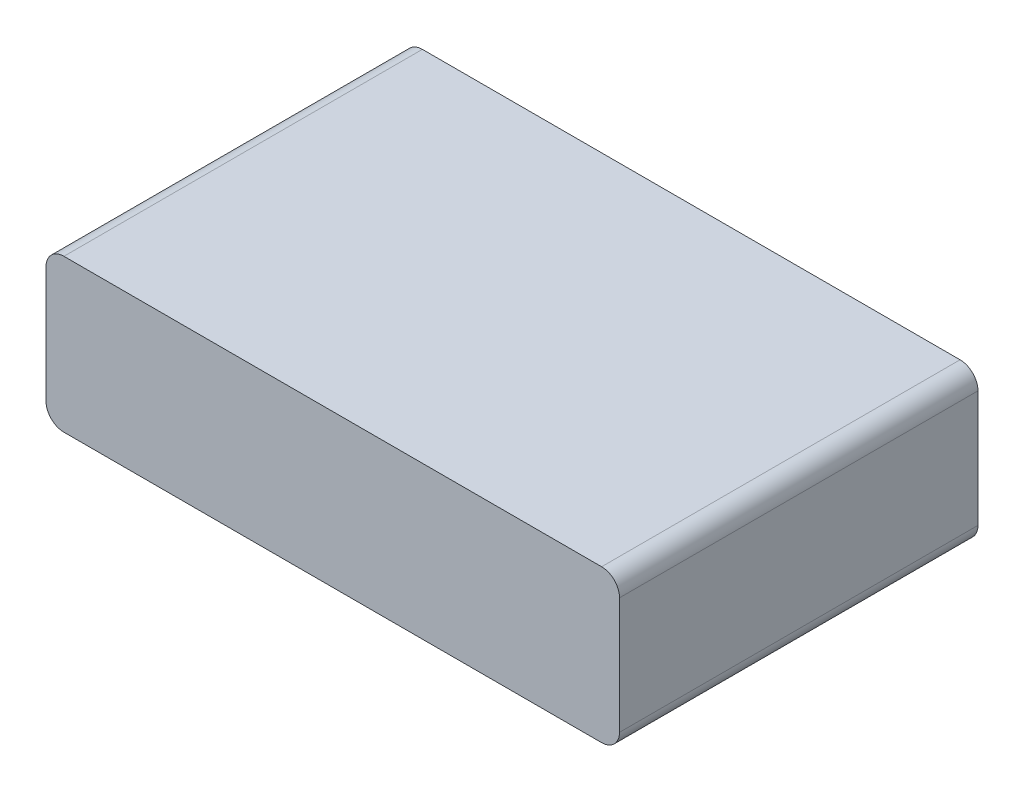
SolidWorks part; units mm, degrees
material "PVC 0.007 Plasticized"
ref_plane "Front" through (0, 0, 0) normal (0, 0, 1) x (1, 0, 0)
ref_plane "Top" through (0, 0, 0) normal (0, 1, 0) x (1, 0, 0)
ref_plane "Right" through (0, 0, 0) normal (1, 0, 0) x (0, 0, -1)
sketch "Sketch1" plane through (0, 0, 0) normal (0, 1, 0) x (1, 0, 0)
  line L1 (-32, 20) -> (32, 20)
  line L2 (-32, 20) -> (-32, -20)
  line L3 (-32, -20) -> (32, -20)
  line L4 (32, 20) -> (32, -20)
  line L5 (-32, 20) -> (32, -20) construction
  line L6 (-32, -20) -> (32, 20) construction
  point P0 (0, 0)
  dimension "D1" = 64
  dimension "D2" = 40
extrude "Boss-Extrude1" add sketch "Sketch1" along normal mid plane 17
fillet "Fillet1" radius 2 4 edges at (-32, -8.5, 0) (-32, 8.5, 0) (32, -8.5, 0) (32, 8.5, 0)
